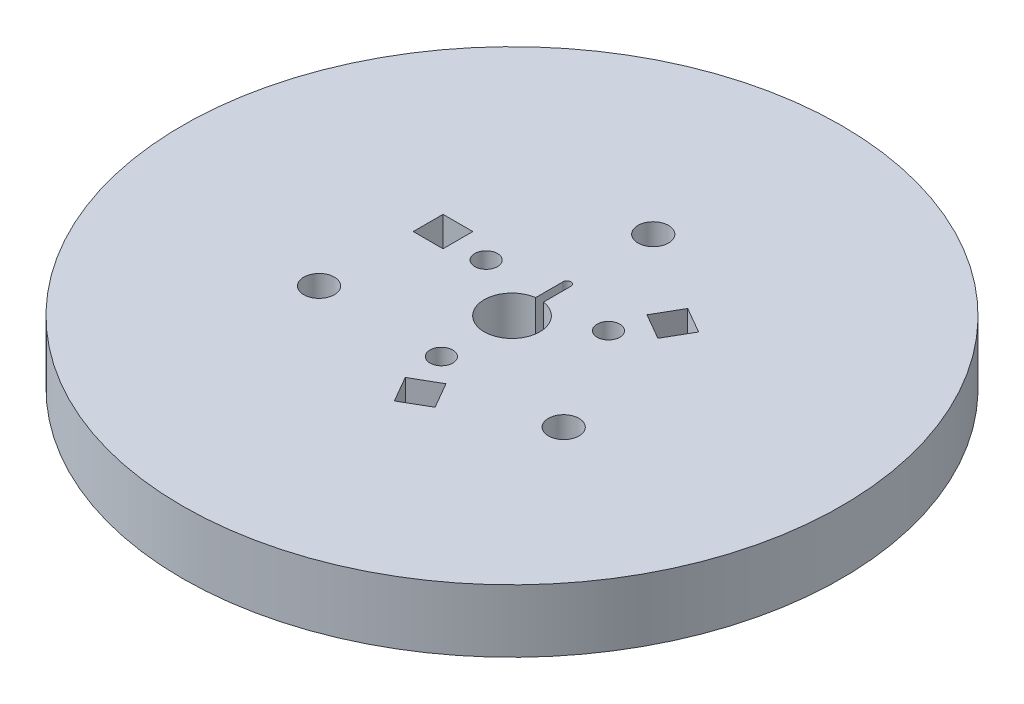
SolidWorks part; units mm, degrees
material "PE Low Density Film"
ref_plane "Front Plane" through (0, 0, 0) normal (0, 0, 1) x (1, 0, 0)
ref_plane "Top Plane" through (0, 0, 0) normal (0, 1, 0) x (1, 0, 0)
ref_plane "Right Plane" through (0, 0, 0) normal (1, 0, 0) x (0, 0, -1)
sketch "Sketch1" plane through (0, 0, 0) normal (0, 1, 0) x (1, 0, 0)
  line L0 (0, 0) -> (0, 18) construction
  line L1 (0, 0) -> (15.5885, -9) construction
  line L2 (0, 0) -> (-15.5885, -9) construction
  line L3 (0, 0) -> (7.7942, 4.5) construction
  line L4 (0, 0) -> (0, -9) construction
  line L5 (0, 0) -> (-7.7942, 4.5) construction
  circle A0 centre (0, 0) radius 42
  circle A2 centre (0, 18) radius 1.95
  circle A3 centre (15.5885, -9) radius 1.95
  circle A4 centre (-15.5885, -9) radius 1.95
  circle A5 centre (0, 0) radius 3.55
  circle A9 centre (7.7942, 4.5) radius 1.45
  circle A10 centre (0, -9) radius 1.45
  circle A11 centre (-7.7942, 4.5) radius 1.45
  dimension "D2" = 3.9
  dimension "D3" = 84
  dimension "D6" = 2.9
  dimension "D9" = 7.1
  dimension "D1" = 18
  dimension "D5" = 60
  dimension "D7" = 9
  dimension "D4" = 3
  dimension "D8" = 3
extrude "Boss-Extrude1" add sketch "Sketch1" along normal blind 8
sketch "Sketch3" plane through (0, 8, 0) normal (0, 1, 0) x (1, 0, 0)
  line L0 (0, 7) -> (0, 0) construction
  line L1 (0.5, 7) -> (0.5, 0)
  line L2 (-0.5, 7) -> (-0.5, 0)
  arc A0 (0.5, 7) -> (-0.5, 7) centre (0, 7) ccw
  arc A1 (-0.5, 0) -> (0.5, 0) centre (0, 0) ccw
  point P2 (0, 3.5)
  dimension "D2" = 0.5
  dimension "D1" = 7
extrude "Cut-Extrude2" cut sketch "Sketch3" against normal blind 10
sketch "Sketch4" plane through (0, 8, 0) normal (0, 1, 0) x (1, 0, 0)
  line L1 (0, 0) -> (0, -18) construction
  line L6 (0, -18) -> (5.1962, -15) construction
  line L8 (1.9053, -16.9) -> (5.1962, -15)
  line L9 (1.9053, -16.9) -> (0.0053, -13.6091)
  line L10 (5.1962, -15) -> (3.2962, -11.7091)
  line L11 (0.0053, -13.6091) -> (3.2962, -11.7091)
  line L12 (-15.5885, 6.8) -> (-15.5885, 3)
  line L13 (-15.5885, 6.8) -> (-11.7885, 6.8)
  line L14 (-15.5885, 3) -> (-11.7885, 3)
  line L15 (-11.7885, 6.8) -> (-11.7885, 3)
  line L16 (0, 0) -> (-15.5885, 9) construction
  line L17 (-15.5885, 9) -> (-15.5885, 3) construction
  line L18 (13.6832, 10.1) -> (10.3923, 12)
  line L19 (13.6832, 10.1) -> (11.7832, 6.8091)
  line L20 (10.3923, 12) -> (8.4923, 8.7091)
  line L21 (11.7832, 6.8091) -> (8.4923, 8.7091)
  line L22 (0, 0) -> (15.5885, 9) construction
  line L23 (15.5885, 9) -> (10.3923, 12) construction
  line L24 (0, 0) -> (3.2962, -11.7091) construction
  line L25 (0, 0) -> (-11.7885, 3) construction
  circle A0 centre (15.5885, -9) radius 10 construction
  dimension "D3" = 120
  dimension "D5" = 20
  dimension "D1" = 18
  dimension "D2" = 60
  dimension "D4" = 3
  dimension "D6" = 90
  dimension "D7" = 6
  dimension "D8" = 3.8
extrude "Cut-Extrude3" cut sketch "Sketch4" against normal blind 35
sketch "Sketch5" plane through (0, 0, 0) normal (0, -1, 0) x (1, 0, 0)
  line L0 (-0.5, -7) -> (-0.5, -3.5146) construction
  line L1 (0.5, -3.5146) -> (0.5, -7) construction
  line L2 (-0.5, -7) -> (-0.5, -3.5146)
  line L3 (0.5, -3.5146) -> (0.5, -7)
  circle A0 centre (0, 0) radius 12
  circle A1 centre (0, 9) radius 1.45 construction
  circle A2 centre (-7.7942, -4.5) radius 1.45 construction
  arc A3 (-0.5, -7) -> (0.5, -7) centre (0, -7) ccw construction
  arc A4 (0.5, -3.5146) -> (-0.5, -3.5146) centre (0, 0) ccw construction
  circle A5 centre (7.7942, -4.5) radius 1.45 construction
  circle A6 centre (0, 9) radius 1.45
  circle A7 centre (-7.7942, -4.5) radius 1.45
  arc A8 (-0.5, -7) -> (0.5, -7) centre (0, -7) ccw
  arc A9 (0.5, -3.5146) -> (-0.5, -3.5146) centre (0, 0) ccw
  circle A10 centre (7.7942, -4.5) radius 1.45
  dimension "D1" = 24
extrude "Boss-Extrude2" add sketch "Sketch5" along normal blind 3
